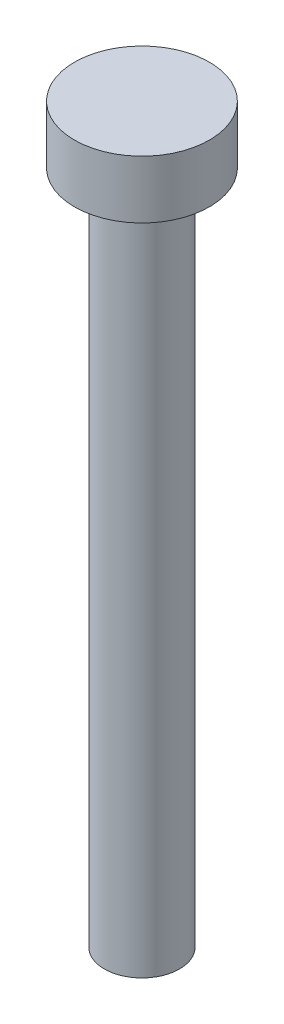
SolidWorks part; units mm, degrees
ref_plane "Front Plane" through (0, 0, 0) normal (0, 0, 1) x (1, 0, 0)
ref_plane "Top Plane" through (0, 0, 0) normal (0, 1, 0) x (1, 0, 0)
ref_plane "Right Plane" through (0, 0, 0) normal (1, 0, 0) x (0, 0, -1)
sketch "Sketch1" plane through (0, 0, 0) normal (0, 1, 0) x (1, 0, 0)
  circle A0 centre (0, 0) radius 3.5
  dimension "D1" = 7
extrude "Boss-Extrude1" add sketch "Sketch1" along normal blind 3
sketch "Sketch2" plane through (0, 0, 0) normal (0, -1, 0) x (1, 0, 0)
  circle A0 centre (0, 0) radius 1.95
  dimension "D1" = 3.9
extrude "Boss-Extrude2" add sketch "Sketch2" along normal blind 35
